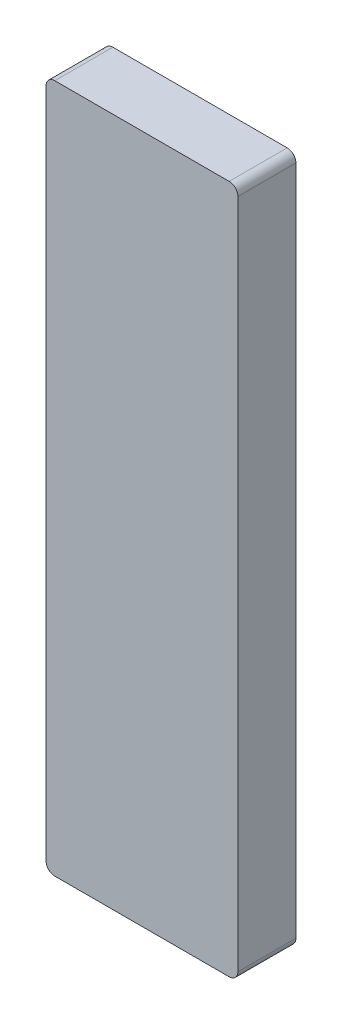
SolidWorks part; units mm, degrees
material "POLYURETHANE (11671)"
ref_plane "Front Plane" through (0, 0, 0) normal (0, 0, 1) x (1, 0, 0)
ref_plane "Top Plane" through (0, 0, 0) normal (0, 1, 0) x (1, 0, 0)
ref_plane "Right Plane" through (0, 0, 0) normal (1, 0, 0) x (0, 0, -1)
sketch "Sketch1" plane through (0, 0, 0) normal (0, 0, 1) x (1, 0, 0)
  line L1 (25.4, 0) -> (533.4, 0)
  line L2 (0, -25.4) -> (0, -1981.2)
  line L3 (25.4, -2006.6) -> (533.4, -2006.6)
  line L4 (558.8, -25.4) -> (558.8, -1981.2)
  arc A0 (0, -1981.2) -> (25.4, -2006.6) centre (25.4, -1981.2) ccw
  arc A1 (533.4, -2006.6) -> (558.8, -1981.2) centre (533.4, -1981.2) ccw
  arc A2 (533.4, 0) -> (558.8, -25.4) centre (533.4, -25.4) cw
  arc A3 (25.4, 0) -> (0, -25.4) centre (25.4, -25.4) ccw
  point P7 (0, -2006.6)
  point P12 (558.8, 0)
  point P15 (0, 0)
  dimension "D3" = 25.4
  dimension "D1" = 2006.6
  dimension "D2" = 558.8
extrude "Boss-Extrude1" add sketch "Sketch1" along normal blind 169.05
ref_plane "Human Mid Plane" through (279.4, 0, 0) normal (1, 0, 0) x (0, 0, -1)
ref_plane "Human Chest Plane" through (0, -1306.6, 0) normal (0, -1, 0) x (-1, 0, 0)
